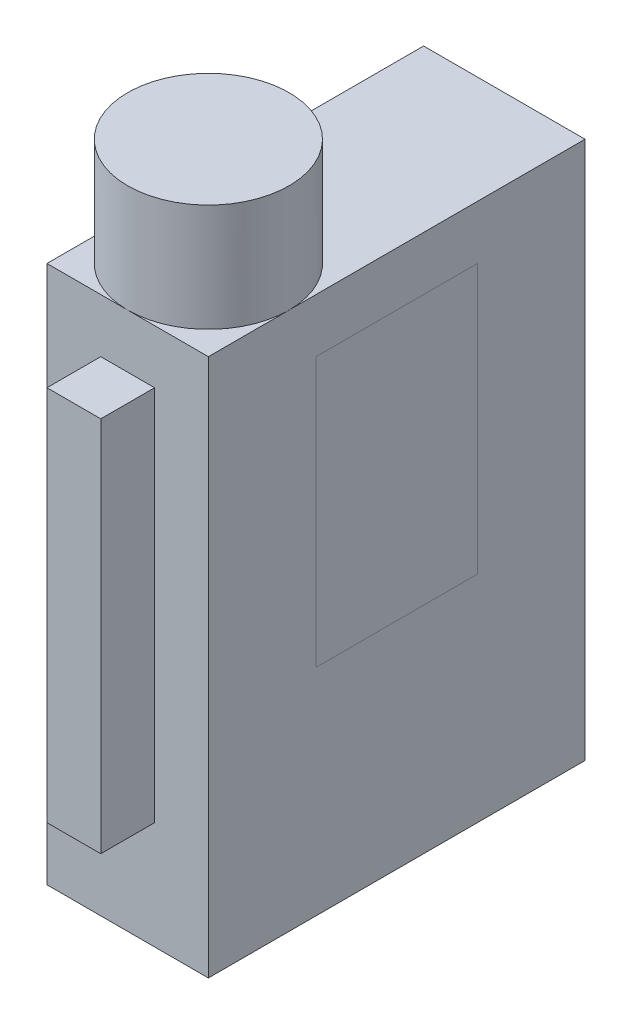
SolidWorks part; units mm, degrees
ref_plane "Front Plane" through (0, 0, 0) normal (0, 0, 1) x (1, 0, 0)
ref_plane "Top Plane" through (0, 0, 0) normal (0, 1, 0) x (1, 0, 0)
ref_plane "Right Plane" through (0, 0, 0) normal (1, 0, 0) x (0, 0, -1)
sketch "Sketch1" plane through (0, 0, 0) normal (0, 0, 1) x (1, 0, 0)
  line L1 (0, 0) -> (30, 0)
  line L2 (0, 0) -> (0, 100)
  line L3 (0, 100) -> (30, 100)
  line L4 (30, 0) -> (30, 100)
  dimension "D1" = 30
  dimension "D2" = 100
extrude "Boss-Extrude1" add sketch "Sketch1" along normal blind 70
sketch "Sketch2" plane through (0, 0, 70) normal (0, 0, 1) x (1, 0, 0)
  line L0 (0, 100) -> (0, 0) construction
  line L1 (10, 90) -> (20, 90)
  line L2 (10, 90) -> (10, 20)
  line L3 (10, 20) -> (20, 20)
  line L4 (20, 90) -> (20, 20)
  line L5 (30, 100) -> (0, 100) construction
  dimension "D1" = 10
  dimension "D2" = 10
  dimension "D3" = 70
  dimension "D4" = 10
extrude "Boss-Extrude2" add sketch "Sketch2" along normal blind 10
sketch "Sketch3" plane through (0, 100, 0) normal (0, 1, 0) x (1, 0, 0)
  line L0 (30, -70) -> (0, -70) construction
  line L3 (0, -70) -> (0, 0) construction
  circle A0 centre (15, -55) radius 15
  dimension "D1" = 30
  dimension "D2" = 15
  dimension "D3" = 15
extrude "Boss-Extrude3" add sketch "Sketch3" along normal blind 20
sketch "Sketch5" plane through (30, 0, 0) normal (1, 0, 0) x (0, 0, -1)
  line L0 (-70, 0) -> (0, 0) construction
  line L1 (-50, 90) -> (-20, 90)
  line L2 (-50, 90) -> (-50, 40)
  line L3 (-50, 40) -> (-20, 40)
  line L4 (-20, 90) -> (-20, 40)
  line L5 (-70, 0) -> (-70, 100) construction
  dimension "D1" = 50
  dimension "D2" = 40
  dimension "D3" = 30
  dimension "D4" = 20
split line "Split Line1"
